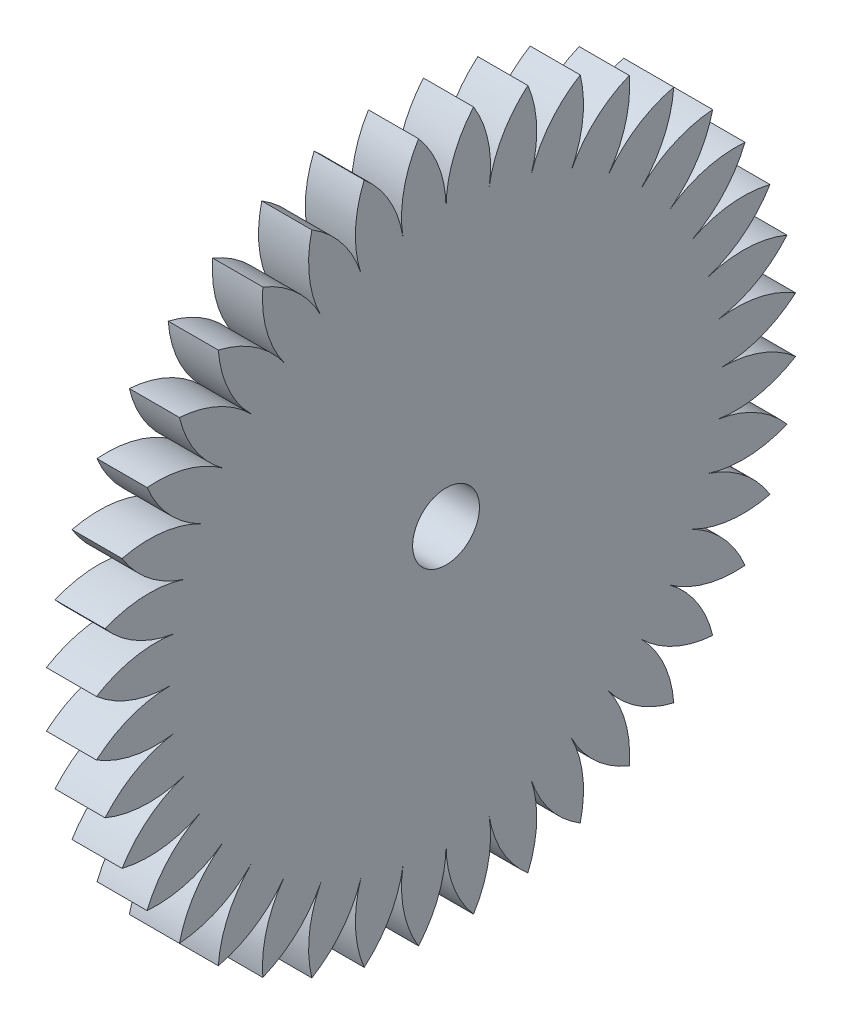
SolidWorks part; units mm, degrees
ref_plane "Front Plane" through (0, 0, 0) normal (0, 0, 1) x (1, 0, 0)
ref_plane "Top Plane" through (0, 0, 0) normal (0, 1, 0) x (1, 0, 0)
ref_plane "Right Plane" through (0, 0, 0) normal (1, 0, 0) x (0, 0, -1)
sketch "Sketch1" plane through (0, 0, 0) normal (1, 0, 0) x (0, 0, -1)
  line L0 (0, 16.5) -> (0, 0)
  line L5 (0, 0) -> (2.5812, 16.2969)
  arc A1 (0, 16.5) -> (1.6476, 20.9353) centre (6.7934, 16.5) cw
  arc A2 (1.6476, 20.9353) -> (2.5812, 16.2969) centre (-4.1286, 17.3596) cw
  dimension "D2" = 21
  dimension "D1" = 16.5
  dimension "D3" = 9
extrude "Boss-Extrude1" add sketch "Sketch1" along normal blind 3
pattern_circular "CirPattern1" count 40 over 360 about axis through (0, 0, 0) along (1, 0, 0) of "Boss-Extrude1"
sketch "Sketch2" plane through (0, 0, 0) normal (1, 0, 0) x (0, 0, -1)
  circle A0 centre (0, 0) radius 2
  dimension "D1" = 4
extrude "Cut-Extrude2" cut sketch "Sketch2" along normal through all
